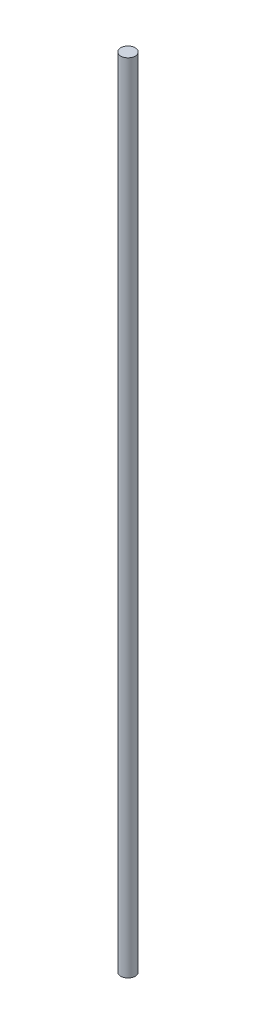
SolidWorks part; units mm, degrees
material "ABS"
ref_plane "Front Plane" through (0, 0, 0) normal (0, 0, 1) x (1, 0, 0)
ref_plane "Top Plane" through (0, 0, 0) normal (0, 1, 0) x (1, 0, 0)
ref_plane "Right Plane" through (0, 0, 0) normal (1, 0, 0) x (0, 0, -1)
sketch "Sketch1" plane through (0, 0, 0) normal (0, 1, 0) x (1, 0, 0)
  circle A0 centre (-18.8416, 0) radius 2
  dimension "D1" = 4
extrude "Boss-Extrude1" add sketch "Sketch1" along normal blind 220 contours A0
